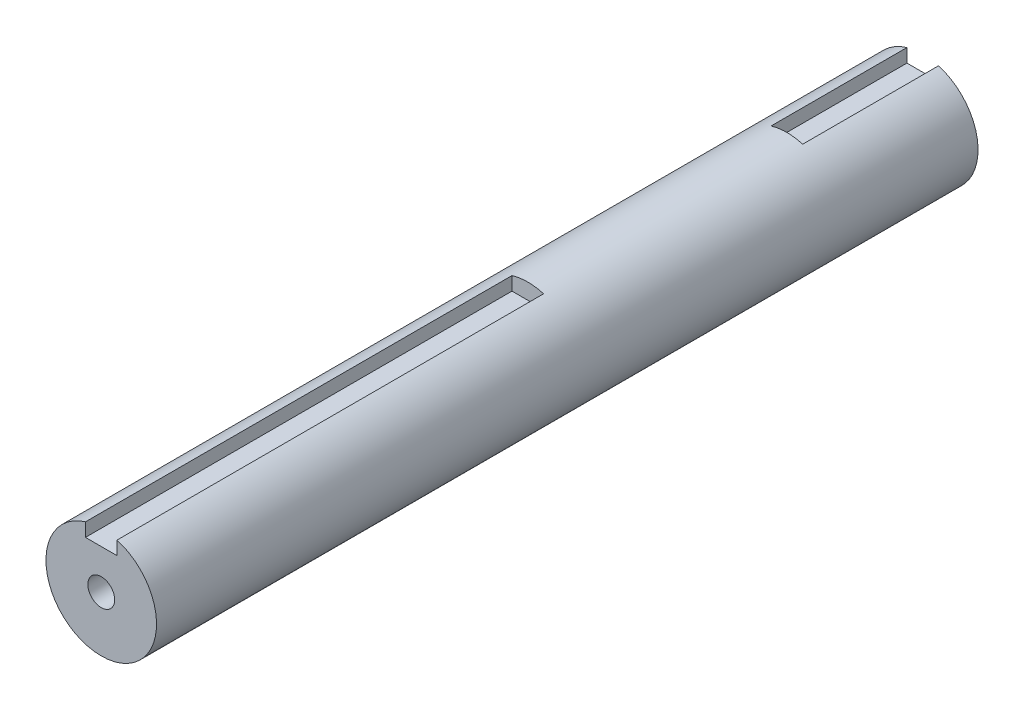
SolidWorks part; units mm, degrees
ref_plane "Plan de face" through (0, 0, 0) normal (0, 0, 1) x (1, 0, 0)
ref_plane "Plan de dessus" through (0, 0, 0) normal (0, 1, 0) x (1, 0, 0)
ref_plane "Plan de droite" through (0, 0, 0) normal (1, 0, 0) x (0, 0, -1)
sketch "Esquisse1" plane through (0, 0, 0) normal (0, 0, 1) x (1, 0, 0)
  circle A0 centre (0, 0) radius 17.5
  dimension "D1" = 35
extrude "Boss.-Extru.1" add sketch "Esquisse1" along normal blind 260
sketch "Esquisse2" plane through (0, 0, 260) normal (0, 0, 1) x (1, 0, 0)
  line L0 (0, 0) -> (0, 17.5) construction
  line L2 (-5, 18.1341) -> (5, 18.1341)
  line L3 (-5, 18.1341) -> (-5, 12.5)
  line L4 (-5, 12.5) -> (5, 12.5)
  line L5 (5, 18.1341) -> (5, 12.5)
  circle A0 centre (0, 0) radius 17.5 construction
  point P10 (0, 12.5)
  point P11 (0, 12.4398)
  dimension "D1" = 10
  dimension "D2" = 5
extrude "Enlèv. mat.-Extru.1" cut sketch "Esquisse2" against normal blind 135
sketch "Esquisse3" plane through (0, 0, 0) normal (0, 0, -1) x (-1, 0, 0)
  line L0 (0, 0) -> (0, 17.5) construction
  line L2 (-5, 18.468) -> (5, 18.468)
  line L3 (-5, 18.468) -> (-5, 12.5)
  line L4 (-5, 12.5) -> (5, 12.5)
  line L5 (5, 18.468) -> (5, 12.5)
  circle A0 centre (0, 0) radius 17.5 construction
  point P10 (0, 12.5)
  point P11 (0, 11.8273)
  dimension "D1" = 10
  dimension "D2" = 5
extrude "Enlèv. mat.-Extru.2" cut sketch "Esquisse3" against normal blind 43
hole_wizard "Trou taraudé M101" positions "Esquisse4" profile "Esquisse5" tap size "M10" standard "ISO"
sketch "Esquisse4" plane through (0, 0, 260) normal (0, 0, 1) x (1, 0, 0)
  point P0 (0, 0)
sketch "Esquisse5" plane through (0, 0, 260) normal (1, 0, 0) x (0, -1, 0)
  line L0 (0, 0) -> (0, 48.5537)
  line L1 (0, 48.5537) -> (4.25, 46)
  line L2 (4.25, 46) -> (4.25, 0)
  line L5 (4.25, 0) -> (0, 0)
  line L10 (0, 48.5537) -> (-4.25, 46) construction
  line L11 (0, -6.35) -> (0, 107.95) construction
  dimension "Diamètre du trou pour taraudage" = 8.5
  dimension "Profondeur du trou pour taraudage" = 46
  dimension "Angle de pointe" = 118
cosmetic thread "Filetage de perçage2" parameters "D1"=38.5, "D2"=10
